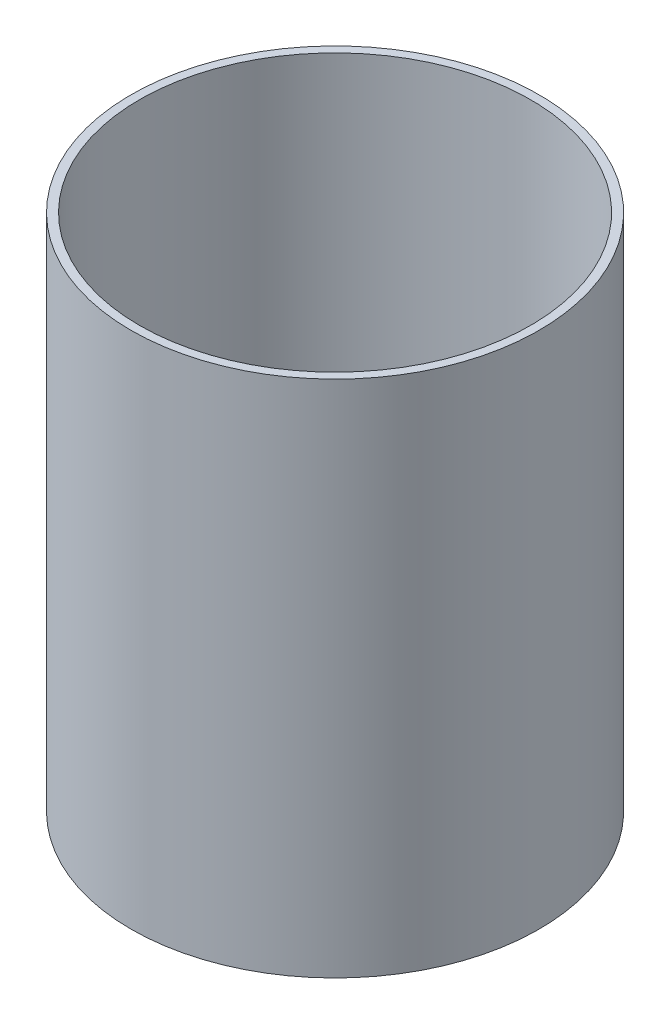
SolidWorks part; units mm, degrees
material "PC High Viscosity"
ref_plane "Front Plane" through (0, 0, 0) normal (0, 0, 1) x (1, 0, 0)
ref_plane "Top Plane" through (0, 0, 0) normal (0, 1, 0) x (1, 0, 0)
ref_plane "Right Plane" through (0, 0, 0) normal (1, 0, 0) x (0, 0, -1)
sketch "Sketch1" plane through (0, 0, 0) normal (0, 1, 0) x (1, 0, 0)
  circle A0 centre (0, 0) radius 73.025
  circle A1 centre (0, 0) radius 76.2
  dimension "D1" = 152.4
  dimension "D2" = 3.175
extrude "Boss-Extrude1" add sketch "Sketch1" along normal blind 193.675
sketch "Sketch2" plane through (0, 193.675, 0) normal (0, 1, 0) x (1, 0, 0)
  line L0 (-51.6365, 6.7352) -> (6.7352, -51.6365) construction
  line L1 (-51.6365, 51.6365) -> (-51.6365, -51.6365)
  line L2 (-6.7352, 51.6365) -> (51.6365, -6.7352) construction
  line L3 (-51.6365, -51.6365) -> (51.6365, -51.6365)
  line L5 (-51.6365, 51.6365) -> (51.6365, 51.6365)
  line L7 (-51.6365, 51.6365) -> (51.6365, -51.6365) construction
  line L8 (51.6365, 51.6365) -> (51.6365, -51.6365)
  circle A1 centre (0, 0) radius 73.025 construction
  dimension "D1" = 31.75
  dimension "D2" = 146.05
  dimension "D3" = 82.55
